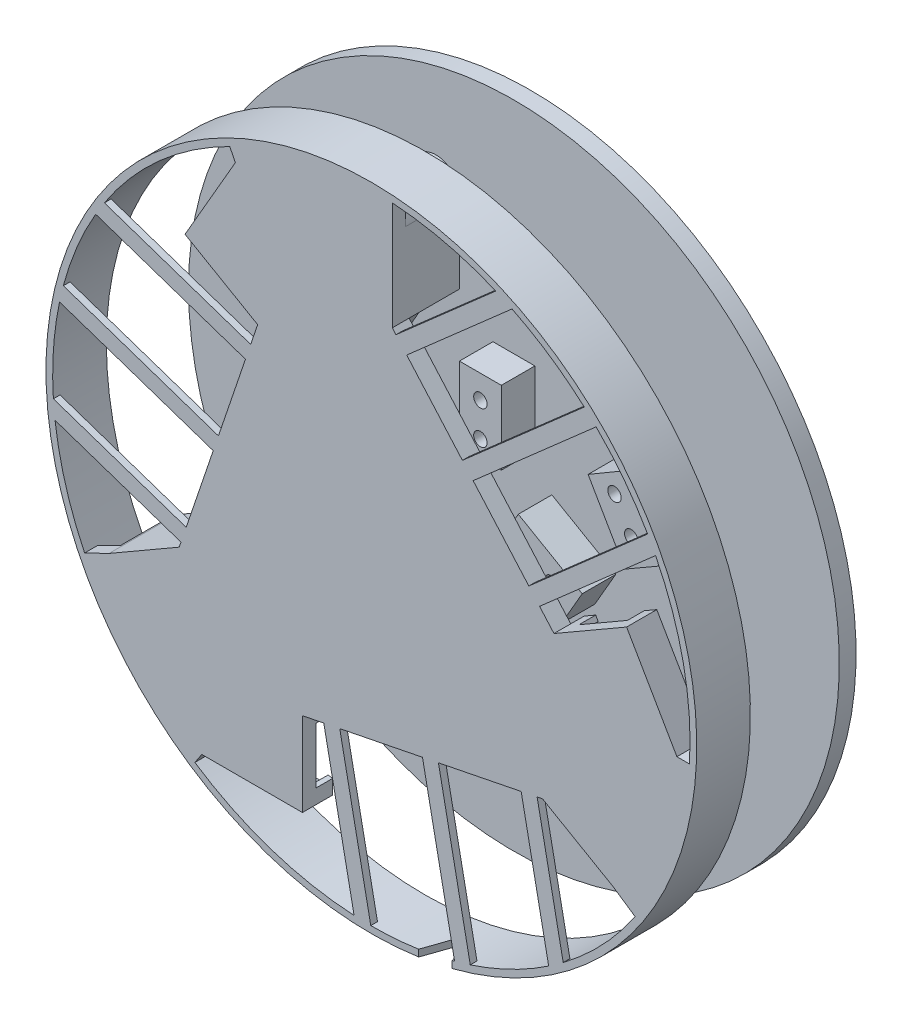
SolidWorks part; units mm, degrees
ref_plane "Alzado" through (0, 0, 0) normal (0, 0, 1) x (1, 0, 0)
ref_plane "Planta" through (0, 0, 0) normal (0, 1, 0) x (1, 0, 0)
ref_plane "Vista lateral" through (0, 0, 0) normal (1, 0, 0) x (0, 0, -1)
sketch "Croquis1" plane through (0, 0, 0) normal (0, 0, 1) x (1, 0, 0)
  line L4 (-284.6174, -30.3598) -> (-262.6174, -30.3598) construction
  line L13 (-262.6174, -17.8598) -> (-266.249, -17.8598) construction
  line L18 (-262.6174, -17.8598) -> (-262.6174, -30.3598) construction
  line L23 (-277.4005, -17.8598) -> (-284.5311, -17.8598) construction
  line L24 (-262.6174, -24.1098) -> (-284.5743, -24.1098) construction
  line L25 (-284.6174, -30.3598) -> (-284.5311, -17.8598) construction
  line L26 (-269.354, -5.2187) -> (-263.104, -16.044) construction
  line L27 (-284.6174, -30.3598) -> (-277.4005, -17.8598) construction
  line L35 (-252.0942, 76.5108) -> (-97.0942, 76.5108) construction
  line L36 (-97.0942, 76.5108) -> (-174.5942, 210.7447) construction
  line L37 (-174.5942, 210.7447) -> (-252.0942, 76.5108) construction
  line L38 (-282.1565, -12.6102) -> (-288.3318, -16.1755) construction
  line L39 (-282.1565, -27.044) -> (-288.3318, -16.1755) construction
  line L47 (-282.1565, -27.044) -> (-282.1565, -12.6102) construction
  line L48 (-282.1565, -12.6102) -> (-288.3318, -16.1755) construction
  line L49 (-266.229, -10.6313) -> (-285.2441, -21.6098) construction
  line L50 (-269.354, -5.2187) -> (-282.1565, -12.6102) construction
  line L51 (-266.229, -10.6313) -> (-285.2441, -21.6098) construction
  line L53 (-153.7083, -83.7331) -> (-164.7083, -64.6806) construction
  line L55 (-175.5336, -70.9306) -> (-173.7178, -74.0756) construction
  line L58 (-175.5336, -70.9306) -> (-164.7083, -64.6806) construction
  line L60 (-183.1128, -83.0851) -> (-176.8628, -72.2598) construction
  line L62 (-170.3103, -90.4767) -> (-164.135, -94.042) construction
  line L65 (-183.1128, -83.0851) -> (-170.3103, -90.4767) construction
  line L70 (-173.7178, -74.0756) -> (-176.8628, -72.2598) construction
  line L72 (-164.135, -94.042) -> (-162.1915, -95.164) construction
  line L73 (-152.6294, -85.6018) -> (-153.7083, -83.7331) construction
  line L75 (-168.142, -83.7331) -> (-164.5767, -89.9084) construction
  line L77 (-170.1209, -67.8056) -> (-159.1425, -86.8208) construction
  line L82 (-153.7083, -83.7331) -> (-164.5767, -89.9084) construction
  line L84 (-153.7083, -83.7331) -> (-168.142, -83.7331) construction
  line L85 (-170.3103, -90.4767) -> (-164.135, -94.042) construction
  line L87 (-157.8103, -83.2598) -> (-164.135, -94.042) construction
  line L88 (-285.2441, -21.6098) -> (-289.5743, -24.1098) construction
  line L89 (-284.5743, -24.1098) -> (-289.5743, -24.1098) construction
  line L90 (-266.249, -17.8598) -> (-263.104, -16.044) construction
  line L91 (-288.3318, -16.1755) -> (-290.2752, -17.2976) construction
  line L92 (-286.7752, -30.3598) -> (-284.6174, -30.3598) construction
  line L93 (-266.249, -17.8598) -> (-282.1565, -27.044) construction
  line L94 (-277.4005, -17.8598) -> (-266.249, -17.8598) construction
  line L95 (-157.8103, -83.2598) -> (-170.3103, -90.4767) construction
  line L96 (-179.9878, -77.6725) -> (-160.9726, -88.6509) construction
  line L97 (-179.9878, -77.6725) -> (-160.9726, -88.6509) construction
  line L98 (-160.9726, -88.6509) -> (-156.6425, -91.1509) construction
  line L99 (-159.1425, -86.8208) -> (-156.6425, -91.1509) construction
  line L100 (-173.7178, -74.0756) -> (-157.8103, -83.2598) construction
  line L101 (-168.142, -83.7331) -> (-173.7178, -74.0756) construction
  line L124 (-135.8442, 143.6277) -> (-252.0942, 76.5108) construction
  line L125 (-97.0942, 76.5108) -> (-213.3442, 143.6277) construction
  line L126 (-174.5942, 210.7447) -> (-174.5942, 76.5108) construction
  line L127 (-250.8517, 84.445) -> (-252.7951, 83.323)
  line L128 (-228.7489, 89.9892) -> (-247.7641, 79.0108) construction
  line L129 (-244.6764, 73.5765) -> (-250.8517, 84.445) construction
  line L130 (-228.7489, 89.9892) -> (-247.7641, 79.0108) construction
  line L137 (-231.8739, 95.4019) -> (-225.6239, 84.5765)
  line L138 (-231.8739, 95.4019) -> (-244.6764, 88.0103)
  line L139 (-225.1373, 76.5108) -> (-247.0942, 76.5108) construction
  line L140 (-247.7641, 79.0108) -> (-252.0942, 76.5108) construction
  line L142 (-247.0942, 76.5108) -> (-252.0942, 76.5108) construction
  line L143 (-244.6764, 73.5765) -> (-244.6764, 88.0103) construction
  line L144 (-247.1373, 70.2608) -> (-239.9205, 82.7608) construction
  line L146 (-225.1373, 82.7608) -> (-225.1373, 70.2608)
  line L148 (-247.1373, 70.2608) -> (-225.1373, 70.2608)
  line L149 (-228.7689, 82.7608) -> (-244.6764, 73.5765) construction
  line L150 (-225.1373, 82.7608) -> (-228.7689, 82.7608)
  line L151 (-228.7689, 82.7608) -> (-225.6239, 84.5765)
  line L152 (-244.6764, 88.0103) -> (-250.8517, 84.445)
  line L155 (-247.1373, 70.2608) -> (-247.051, 82.7608) construction
  line L156 (-244.6764, 88.0103) -> (-250.8517, 84.445) construction
  line L158 (-249.2951, 70.2608) -> (-247.1373, 70.2608)
  line L159 (-239.9205, 82.7608) -> (-247.051, 82.7608) construction
  line L161 (-239.9205, 82.7608) -> (-228.7689, 82.7608) construction
  line L162 (-180.8442, 187.4194) -> (-180.8442, 183.7879)
  line L165 (-168.3442, 183.7879) -> (-180.8442, 183.7879)
  line L167 (-168.3442, 198.571) -> (-168.3442, 205.7016) construction
  line L169 (-174.5942, 205.7447) -> (-174.5942, 210.7447) construction
  line L170 (-168.3442, 205.7016) -> (-168.3442, 207.9457)
  line L172 (-175.2684, 197.077) -> (-171.7031, 203.2522) construction
  line L173 (-188.0726, 187.3994) -> (-177.0942, 206.4146) construction
  line L175 (-174.5942, 183.7879) -> (-174.5942, 205.7447) construction
  line L176 (-168.3442, 198.571) -> (-168.3442, 205.7016)
  line L177 (-177.0942, 206.4146) -> (-174.5942, 210.7447) construction
  line L178 (-174.5942, 183.7879) -> (-174.5942, 205.7447) construction
  line L180 (-180.8442, 205.7879) -> (-168.3442, 205.7016) construction
  line L182 (-182.4853, 209.577) -> (-171.7031, 203.2522) construction
  line L183 (-180.8442, 187.4194) -> (-180.8442, 205.7879) construction
  line L185 (-168.3442, 183.7879) -> (-168.3442, 198.571)
  line L186 (-182.4853, 209.577) -> (-193.4853, 190.5244)
  line L189 (-182.4853, 209.577) -> (-175.2684, 197.077) construction
  line L191 (-175.2684, 197.077) -> (-180.8442, 187.4194) construction
  line L194 (-182.6599, 184.2744) -> (-180.8442, 187.4194)
  line L195 (-182.6599, 184.2744) -> (-193.4853, 190.5244)
  line L196 (-180.8442, 205.7879) -> (-168.3442, 198.571) construction
  line L197 (-181.4064, 211.4457) -> (-182.4853, 209.577)
  line L198 (-94.1599, 83.9285) -> (-108.5937, 83.9285) construction
  line L199 (-123.5645, 84.5765) -> (-110.7619, 77.185)
  line L200 (-110.7619, 77.185) -> (-104.5867, 73.6197) construction
  line L205 (-98.2619, 84.4019) -> (-104.5867, 73.6197) construction
  line L206 (-101.4243, 79.0108) -> (-97.0942, 76.5108) construction
  line L207 (-104.5867, 73.6197) -> (-102.6432, 72.4976)
  line L208 (-99.5942, 80.8409) -> (-97.0942, 76.5108) construction
  line L209 (-94.1599, 83.9285) -> (-105.1599, 102.9811)
  line L210 (-120.4395, 89.9892) -> (-101.4243, 79.0108) construction
  line L211 (-115.9853, 96.7311) -> (-105.1599, 102.9811)
  line L212 (-114.1695, 93.5861) -> (-117.3145, 95.4019)
  line L213 (-98.2619, 84.4019) -> (-110.7619, 77.185) construction
  line L214 (-93.081, 82.0598) -> (-94.1599, 83.9285)
  line L215 (-108.5937, 83.9285) -> (-114.1695, 93.5861) construction
  line L216 (-108.5937, 83.9285) -> (-105.0284, 77.7533) construction
  line L217 (-110.5726, 99.8561) -> (-99.5942, 80.8409) construction
  line L218 (-114.1695, 93.5861) -> (-98.2619, 84.4019) construction
  line L219 (-120.4395, 89.9892) -> (-101.4243, 79.0108) construction
  line L220 (-110.7619, 77.185) -> (-104.5867, 73.6197)
  line L221 (-94.1599, 83.9285) -> (-105.0284, 77.7533) construction
  line L222 (-123.5645, 84.5765) -> (-117.3145, 95.4019)
  line L223 (-115.9853, 96.7311) -> (-114.1695, 93.5861)
  line L224 (-247.7641, 79.0108) -> (-174.5942, 121.2554) construction
  line L225 (-247.7641, 79.0108) -> (-182.6599, 116.5987) construction
  line L226 (-102.6432, -54.2286) -> (-102.6432, -47.098) construction
  line L227 (-111.3932, -46.385) -> (-108.8932, -42.0549) construction
  line L228 (-116.959, -68.5252) -> (-115.1432, -65.3802) construction
  line L229 (-115.7054, -41.3539) -> (-116.7843, -43.2226) construction
  line L230 (-116.7843, -43.2226) -> (-109.5674, -55.7226) construction
  line L231 (-115.1432, -47.0117) -> (-102.6432, -54.2286) construction
  line L232 (-109.5674, -55.7226) -> (-106.0021, -49.5474) construction
  line L233 (-115.1432, -65.3802) -> (-115.1432, -69.0117) construction
  line L234 (-115.1432, -65.3802) -> (-115.1432, -47.0117) construction
  line L235 (-102.6432, -54.2286) -> (-102.6432, -47.098) construction
  line L236 (-108.8932, -47.0549) -> (-108.8932, -42.0549) construction
  line L237 (-102.6432, -69.0117) -> (-115.1432, -69.0117) construction
  line L238 (-108.8932, -69.0117) -> (-108.8932, -47.0549) construction
  line L239 (-102.6432, -69.0117) -> (-102.6432, -54.2286) construction
  line L240 (-109.5674, -55.7226) -> (-115.1432, -65.3802) construction
  line L241 (-115.1432, -47.0117) -> (-102.6432, -47.098) construction
  line L242 (-108.8932, -69.0117) -> (-108.8932, -47.0549) construction
  line L243 (-116.959, -68.5252) -> (-127.7843, -62.2752) construction
  line L244 (-102.6432, -47.098) -> (-102.6432, -44.8539) construction
  line L245 (-116.7843, -43.2226) -> (-106.0021, -49.5474) construction
  line L246 (-116.7843, -43.2226) -> (-127.7843, -62.2752) construction
  line L247 (-122.3716, -65.4002) -> (-111.3932, -46.385) construction
  line L248 (-172.9402, 56.3242) -> (-183.9402, 37.2716) construction
  line L249 (-173.1149, 31.0216) -> (-171.2991, 34.1666) construction
  line L250 (-173.1149, 31.0216) -> (-183.9402, 37.2716) construction
  line L251 (-158.7991, 30.5351) -> (-171.2991, 30.5351) construction
  line L252 (-158.7991, 45.3182) -> (-158.7991, 52.4488) construction
  line L253 (-158.7991, 30.5351) -> (-158.7991, 45.3182) construction
  line L254 (-171.2991, 34.1666) -> (-171.2991, 30.5351) construction
  line L255 (-158.7991, 52.4488) -> (-158.7991, 54.6929) construction
  line L256 (-171.8613, 58.1929) -> (-172.9402, 56.3242) construction
  line L257 (-165.7233, 43.8242) -> (-162.158, 49.9995) construction
  line L258 (-178.5275, 34.1466) -> (-167.5491, 53.1618) construction
  line L259 (-172.9402, 56.3242) -> (-162.158, 49.9995) construction
  line L260 (-172.9402, 56.3242) -> (-165.7233, 43.8242) construction
  line L261 (-158.7991, 45.3182) -> (-158.7991, 52.4488) construction
  line L262 (-171.2991, 52.5351) -> (-158.7991, 52.4488) construction
  line L263 (-171.2991, 52.5351) -> (-158.7991, 45.3182) construction
  line L264 (-165.0491, 30.5351) -> (-165.0491, 52.492) construction
  line L265 (-165.0491, 30.5351) -> (-165.0491, 52.492) construction
  line L266 (-165.0491, 52.492) -> (-165.0491, 57.492) construction
  line L267 (-167.5491, 53.1618) -> (-165.0491, 57.492) construction
  line L268 (-171.2991, 34.1666) -> (-171.2991, 52.5351) construction
  line L269 (-165.7233, 43.8242) -> (-171.2991, 34.1666) construction
  circle A2 centre (-269.6174, -24.1098) radius 2 construction
  circle A3 centre (-279.6174, -24.1098) radius 2 construction
  circle A25 centre (-272.2911, -14.1313) radius 2 construction
  circle A26 centre (-280.9514, -19.1313) radius 2 construction
  arc A27 (-286.7752, -30.3598) -> (-290.2752, -17.2976) centre (-286.7752, -23.3598) cw construction
  circle A28 centre (-166.6209, -73.8677) radius 2 construction
  circle A29 centre (-161.6209, -82.528) radius 2 construction
  circle A30 centre (-173.9256, -81.1725) radius 2 construction
  circle A31 centre (-165.2654, -86.1725) radius 2 construction
  arc A32 (-152.6294, -85.6018) -> (-162.1915, -95.164) centre (-158.6915, -89.1018) cw construction
  circle A54 centre (-234.811, 86.4892) radius 2
  circle A55 centre (-243.4713, 81.4892) radius 2
  circle A56 centre (-232.1373, 76.5108) radius 2
  circle A57 centre (-242.1373, 76.5108) radius 2
  arc A58 (-249.2951, 70.2608) -> (-252.7951, 83.323) centre (-249.2951, 77.2608) cw
  circle A59 centre (-179.5726, 202.1218) radius 2
  circle A60 centre (-174.5942, 190.7879) radius 2
  circle A61 centre (-184.5726, 193.4616) radius 2
  arc A62 (-181.4064, 211.4457) -> (-168.3442, 207.9457) centre (-175.3442, 207.9457) cw
  circle A63 centre (-174.5942, 200.7879) radius 2
  circle A64 centre (-102.0726, 85.1337) radius 2
  circle A65 centre (-107.0726, 93.7939) radius 2
  circle A66 centre (-105.7171, 81.4892) radius 2
  circle A67 centre (-114.3773, 86.4892) radius 2
  arc A68 (-93.081, 82.0598) -> (-102.6432, 72.4976) centre (-99.1432, 78.5598) cw
  circle A69 centre (-174.5942, 121.2554) radius 9.3135
  circle A71 centre (-108.8932, -62.0117) radius 2 construction
  circle A72 centre (-118.8716, -59.338) radius 2 construction
  circle A73 centre (-113.8716, -50.6778) radius 2 construction
  circle A74 centre (-108.8932, -52.0117) radius 2 construction
  arc A75 (-115.7054, -41.3539) -> (-102.6432, -44.8539) centre (-109.6432, -44.8539) cw construction
  circle A76 centre (-175.0275, 40.2088) radius 2 construction
  circle A77 centre (-170.0275, 48.8691) radius 2 construction
  circle A78 centre (-165.0491, 37.5351) radius 2 construction
  circle A79 centre (-165.0491, 47.5351) radius 2 construction
  arc A80 (-171.8613, 58.1929) -> (-158.7991, 54.6929) centre (-165.7991, 54.6929) cw construction
  point P1 (-145.4363, 273.9919)
  point P88 (-203.7553, -19.2562)
  dimension "D10" = 30
  dimension "D12" = 4
  dimension "D13" = 5
  dimension "D9" = 7
  dimension "D14" = 5
  dimension "D16" = 7
  dimension "D2" = 5
  dimension "D3" = 60
  dimension "D4" = 5
  dimension "D5" = 30
  dimension "D6" = 22
  dimension "D7" = 60
  dimension "D8" = 155
  dimension "D11" = 10
  dimension "D15" = 30
  dimension "D17" = 30
extrude "Saliente-Extruir2" add sketch "Croquis1" along normal blind 20
sketch "Croquis2" plane through (0, 0, 20) normal (0, 0, 1) x (1, 0, 0)
  line L0 (-105.1599, 102.9811) -> (-120.1599, 128.9619)
  line L1 (-225.1373, 70.2608) -> (-195.1373, 70.2608)
  line L3 (-225.1373, 45.2608) -> (-195.1373, 45.2608)
  line L4 (-195.1373, 70.2608) -> (-195.1373, 45.2608)
  line L5 (-120.1599, 128.9619) -> (-98.5093, 141.4619)
  line L6 (-98.5093, 141.4619) -> (-83.5093, 115.4811)
  line L8 (-193.4853, 190.5244) -> (-208.4853, 164.5436)
  line L9 (-208.4853, 164.5436) -> (-230.1359, 177.0436)
  line L10 (-230.1359, 177.0436) -> (-217.349, 199.1913)
  line L11 (-217.349, 199.1913) -> (-215.1359, 203.0244)
  line L13 (-168.3442, 207.9457) -> (-168.3442, 216.0496)
  line L14 (-215.1359, 203.0244) -> (-216.7938, 206.3682)
  line L15 (-252.7951, 83.323) -> (-260.0693, 79.7945)
  line L16 (-225.1373, 45.2608) -> (-227.2042, 42.1531)
  line L17 (-83.5093, 115.4811) -> (-79.7698, 115.4811)
  line L18 (-102.6432, 72.4976) -> (-95.9504, 67.9623)
  line L19 (-102.6432, 72.4976) -> (-94.499, 84.5159)
  line L20 (-93.081, 82.0598) -> (-105.1599, 102.9811) construction
  line L21 (-94.499, 84.5159) -> (-105.1599, 102.9811)
  line L22 (-225.1373, 70.2608) -> (-249.2951, 70.2608)
  line L23 (-249.2951, 70.2608) -> (-252.7951, 83.323)
  line L24 (-193.4853, 190.5244) -> (-182.6599, 184.2744)
  line L25 (-182.6599, 184.2744) -> (-180.8442, 187.4194)
  line L26 (-180.8442, 187.4194) -> (-180.8442, 183.7879)
  line L27 (-180.8442, 183.7879) -> (-168.3442, 183.7879)
  line L28 (-168.3442, 183.7879) -> (-168.3442, 207.9457)
  arc A0 (-79.7698, 115.4811) -> (-168.3442, 216.0496) centre (-174.5942, 121.2554) ccw
  circle A1 centre (-174.5942, 121.2554) radius 97
  arc A2 (-216.7938, 206.3682) -> (-260.0693, 79.7945) centre (-174.5942, 121.2554) ccw
  arc A3 (-227.2042, 42.1531) -> (-95.9504, 67.9623) centre (-174.5942, 121.2554) ccw
  dimension "D1" = 190
  dimension "D2" = 2
  dimension "D3" = 30
  dimension "D4" = 25
  dimension "D5" = 30
  dimension "D6" = 25
  dimension "D7" = 30
  dimension "D8" = 25
  dimension "D9" = 30
extrude "Saliente-Extruir3" add sketch "Croquis2" against normal blind 4
sketch "Croquis3" plane through (0, 0, 0) normal (0, 0, -1) x (-1, 0, 0)
  circle A0 centre (174.5942, 200.7879) radius 2
  circle A3 centre (179.5726, 202.1218) radius 2
  circle A4 centre (184.5726, 193.4616) radius 2
  circle A5 centre (174.5942, 190.7879) radius 2
extrude "Cortar-Extruir2" cut sketch "Croquis3" against normal blind 36
sketch "Croquis4" plane through (0, 0, 20) normal (0, 0, 1) x (1, 0, 0)
  line L0 (-110.746, 83.0522) -> (-110.7165, 81.4124)
  line L1 (-173.4333, 195.6512) -> (-172.0279, 196.4967)
  line L2 (-107.0309, 88.7941) -> (-109.4032, 86.9969)
  line L3 (-180.2635, 195.9976) -> (-177.5209, 194.8418)
  line L4 (-183.5776, 199.1284) -> (-183.7476, 198.393)
  line L5 (-102.6625, 90.0987) -> (-103.2144, 90.6137)
  line L6 (-239.6033, 85.0629) -> (-241.0381, 85.8572)
  line L7 (-236.4882, 78.9745) -> (-236.8585, 81.9276)
  line L8 (-237.5425, 74.5391) -> (-236.8206, 74.7596)
  arc A0 (-183.7476, 198.393) -> (-180.2635, 195.9976) centre (-184.5726, 193.4616) ccw
  arc A1 (-177.5209, 194.8418) -> (-173.4333, 195.6512) centre (-174.5942, 190.7879) ccw
  arc A2 (-175.9744, 205.5936) -> (-183.5776, 199.1284) centre (-179.5726, 202.1218) ccw
  arc A4 (-103.2144, 90.6137) -> (-107.0309, 88.7941) centre (-107.0726, 93.7939) ccw
  arc A5 (-109.4032, 86.9969) -> (-110.746, 83.0522) centre (-114.3773, 86.4892) ccw
  arc A6 (-172.0279, 196.4967) -> (-175.9744, 205.5936) centre (-174.5942, 200.7879) ccw
  arc A7 (-100.8651, 80.2817) -> (-102.6625, 90.0987) centre (-102.0726, 85.1337) ccw
  arc A8 (-110.7165, 81.4124) -> (-100.8651, 80.2817) centre (-105.7171, 81.4892) ccw
  arc A9 (-236.8206, 74.7596) -> (-236.4882, 78.9745) centre (-232.1373, 76.5108) ccw
  arc A10 (-236.8585, 81.9276) -> (-239.6033, 85.0629) centre (-234.811, 86.4892) ccw
  arc A11 (-246.943, 77.891) -> (-237.5425, 74.5391) centre (-242.1373, 76.5108) ccw
  arc A12 (-241.0381, 85.8572) -> (-246.943, 77.891) centre (-243.4713, 81.4892) ccw
  point P40 (-174.5942, 121.2554)
  dimension "D1" = 10
  dimension "D2" = 10
  dimension "D3" = 3
sketch "Croquis5" plane through (0, 0, 16) normal (0, 0, -1) x (-1, 0, 0)
  line L1 (83.5093, 115.4811) -> (98.5093, 141.4619)
  line L2 (98.5093, 141.4619) -> (102.2503, 139.302)
  line L3 (120.1599, 128.9619) -> (98.5093, 141.4619) construction
  line L4 (116.7163, 130.95) -> (120.1599, 128.9619)
  line L5 (120.1599, 128.9619) -> (96.8471, 88.5828)
  line L6 (98.5093, 137.5214) -> (84.7655, 113.7667)
  line L7 (98.5093, 137.5214) -> (99.5395, 139.302)
  line L8 (99.5395, 139.302) -> (101.7362, 138.0311)
  line L9 (101.7362, 138.0311) -> (102.2503, 139.302)
  line L11 (116.7163, 130.95) -> (115.9702, 129.6577)
  line L12 (115.9702, 129.6577) -> (118.0912, 128.4331)
  line L13 (118.0912, 128.4331) -> (95.5245, 89.3464)
  line L14 (95.5245, 89.3464) -> (96.8471, 88.5828)
  line L16 (116.7163, 130.95) -> (120.1599, 128.9619)
  line L17 (215.1359, 203.0244) -> (230.1359, 177.0436)
  line L18 (230.1359, 177.0436) -> (226.3949, 174.8838)
  line L19 (211.9289, 166.5318) -> (208.4853, 164.5436)
  line L20 (208.4853, 164.5436) -> (185.1724, 204.9227)
  line L21 (226.7233, 179.0139) -> (213.0231, 202.7937)
  line L22 (226.7233, 179.0139) -> (227.7503, 177.2314)
  line L23 (227.7503, 177.2314) -> (225.5514, 175.9645)
  line L24 (225.5514, 175.9645) -> (226.3949, 174.8838)
  line L25 (211.9289, 166.5318) -> (211.1828, 167.8242)
  line L26 (211.1828, 167.8242) -> (209.0617, 166.5996)
  line L27 (209.0617, 166.5996) -> (186.495, 205.6863)
  line L28 (186.495, 205.6863) -> (185.1724, 204.9227)
  line L30 (211.9289, 166.5318) -> (208.4853, 164.5436)
  line L32 (225.1373, 45.2608) -> (195.1373, 45.2608)
  line L33 (195.1373, 45.2608) -> (195.1373, 49.5805)
  line L34 (195.1373, 66.2844) -> (195.1373, 70.2608)
  line L35 (195.1373, 70.2608) -> (241.763, 70.2608)
  line L36 (198.5499, 47.231) -> (225.994, 47.2058)
  line L37 (198.5499, 47.231) -> (196.4927, 47.2329)
  line L38 (196.4927, 47.2329) -> (196.495, 49.7707)
  line L39 (196.495, 49.7707) -> (195.1373, 49.5805)
  line L40 (195.1373, 66.2844) -> (196.6296, 66.2844)
  line L41 (196.6296, 66.2844) -> (196.6296, 68.7336)
  line L42 (196.6296, 68.7336) -> (241.763, 68.7336)
  line L43 (241.763, 68.7336) -> (241.763, 70.2608)
  line L45 (195.1373, 66.2844) -> (195.1373, 70.2608)
  line L48 (225.1373, 45.2608) -> (225.994, 47.2058)
  line L49 (83.5093, 115.4811) -> (84.7655, 113.7667)
  line L50 (215.1359, 203.0244) -> (213.0231, 202.7937)
  point P51 (174.5942, 121.2554)
  line M15 (93.081, 82.0598) -> (105.1599, 102.9811)
  line M16 (105.1599, 102.9811) -> (120.1599, 128.9619)
  line M17 (120.1599, 128.9619) -> (98.5093, 141.4619)
  line M23 (181.4064, 211.4457) -> (193.4853, 190.5244)
  line M24 (193.4853, 190.5244) -> (208.4853, 164.5436)
  line M25 (208.4853, 164.5436) -> (230.1359, 177.0436)
  line M26 (230.1359, 177.0436) -> (215.1359, 203.0244)
  line M31 (249.2951, 70.2608) -> (225.1373, 70.2608)
  line M32 (225.1373, 70.2608) -> (195.1373, 70.2608)
  line M33 (195.1373, 70.2608) -> (195.1373, 45.2608)
  dimension "D1" = 3
extrude "Saliente-Extruir6" add sketch "Croquis5" along normal blind 5 contours L42 L43 L40 L41 M31 M32 M33 | L13 L14 L11 L12 M15 M16 M17 | L27 L28 L25 L26 M23 M24 M25 | L50 L21 L22 L23 L24 M26 M25 | L36 L48 L32 L33 L39 L38 L37 | L1 L2 L9 L8 L7 L6 L49
sketch "Croquis6" plane through (0, 0, 16) normal (0, 0, -1) x (-1, 0, 0)
  circle A0 centre (174.5942, 121.2554) radius 97
  circle A1 centre (174.5942, 121.2554) radius 95
extrude "Saliente-Extruir7" add sketch "Croquis6" along normal blind 35
sketch "Croquis7" plane through (0, 0, 20) normal (0, 0, 1) x (1, 0, 0)
  line L1 (-191.2527, 143.6517) -> (-154.7152, 143.6517)
  line L2 (-191.2527, 143.6517) -> (-191.2527, 92.2383)
  line L3 (-191.2527, 92.2383) -> (-154.7152, 92.2383)
  line L4 (-154.7152, 143.6517) -> (-154.7152, 92.2383)
extrude "Cortar-Extruir6" cut sketch "Croquis7" against normal through all
sketch "Croquis9" plane through (0, 0, 20) normal (0, 0, 1) x (1, 0, 0)
  line L1 (-195.1373, 70.2608) -> (-123.5645, 84.5765)
  line L2 (-231.8739, 95.4019) -> (-208.4853, 164.5436)
  line L3 (-208.4853, 164.5436) -> (-193.4853, 190.5244)
  line L4 (-231.8739, 95.4019) -> (-225.6239, 84.5765)
  line L5 (-225.6239, 84.5765) -> (-228.7689, 82.7608)
  line L6 (-228.7689, 82.7608) -> (-225.1373, 82.7608)
  line L7 (-225.1373, 70.2608) -> (-195.1373, 70.2608)
  line L8 (-123.5645, 84.5765) -> (-117.3145, 95.4019)
  line L9 (-117.3145, 95.4019) -> (-114.1695, 93.5861)
  line L10 (-114.1695, 93.5861) -> (-115.9853, 96.7311)
  line L11 (-115.9853, 96.7311) -> (-105.1599, 102.9811)
  line L12 (-105.1599, 102.9811) -> (-120.1599, 128.9619)
  line L13 (-193.4853, 190.5244) -> (-182.6599, 184.2744)
  line L14 (-182.6599, 184.2744) -> (-180.8442, 187.4194)
  line L15 (-180.8442, 187.4194) -> (-180.8442, 183.7879)
  line L16 (-180.8442, 183.7879) -> (-168.3442, 183.7879)
  line L17 (-168.3442, 183.7879) -> (-120.1599, 128.9619)
  line L46 (-102.6432, 72.4976) -> (-123.5645, 84.5765)
  line L47 (-95.9504, 67.9623) -> (-102.6432, 72.4976)
  line L48 (-225.1373, 45.2608) -> (-227.2042, 42.1531)
  line L49 (-195.1373, 45.2608) -> (-225.1373, 45.2608)
  line L50 (-195.1373, 70.2608) -> (-195.1373, 45.2608)
  line L51 (-225.1373, 70.2608) -> (-195.1373, 70.2608)
  line L52 (-225.1373, 82.7608) -> (-225.1373, 70.2608)
  line L53 (-228.7689, 82.7608) -> (-225.1373, 82.7608)
  line L54 (-225.6239, 84.5765) -> (-228.7689, 82.7608)
  line L55 (-231.8739, 95.4019) -> (-225.6239, 84.5765)
  line L56 (-252.7951, 83.323) -> (-231.8739, 95.4019)
  line L57 (-260.0693, 79.7945) -> (-252.7951, 83.323)
  line L58 (-215.1359, 203.0244) -> (-216.7938, 206.3682)
  line L59 (-230.1359, 177.0436) -> (-215.1359, 203.0244)
  line L60 (-208.4853, 164.5436) -> (-230.1359, 177.0436)
  line L61 (-193.4853, 190.5244) -> (-208.4853, 164.5436)
  line L62 (-182.6599, 184.2744) -> (-193.4853, 190.5244)
  line L63 (-180.8442, 187.4194) -> (-182.6599, 184.2744)
  line L64 (-180.8442, 183.7879) -> (-180.8442, 187.4194)
  line L65 (-168.3442, 183.7879) -> (-180.8442, 183.7879)
  line L66 (-168.3442, 216.0496) -> (-168.3442, 183.7879)
  line L67 (-83.5093, 115.4811) -> (-79.7698, 115.4811)
  line L68 (-98.5093, 141.4619) -> (-83.5093, 115.4811)
  line L69 (-120.1599, 128.9619) -> (-98.5093, 141.4619)
  line L70 (-105.1599, 102.9811) -> (-120.1599, 128.9619)
  line L71 (-115.9853, 96.7311) -> (-105.1599, 102.9811)
  line L72 (-114.1695, 93.5861) -> (-115.9853, 96.7311)
  line L73 (-117.3145, 95.4019) -> (-114.1695, 93.5861)
  line L74 (-123.5645, 84.5765) -> (-117.3145, 95.4019)
  line L81 (-225.1373, 82.7608) -> (-225.1373, 70.2608)
  arc A3 (-227.2042, 42.1531) -> (-95.9504, 67.9623) centre (-174.5942, 121.2554) ccw
  arc A4 (-216.7938, 206.3682) -> (-260.0693, 79.7945) centre (-174.5942, 121.2554) ccw
  arc A5 (-79.7698, 115.4811) -> (-168.3442, 216.0496) centre (-174.5942, 121.2554) ccw
  dimension "D1" = 0
extrude "Saliente-Extruir13" add sketch "Croquis9" against normal blind 3
sketch "Croquis12" plane through (0, 0, 20) normal (0, 0, 1) x (1, 0, 0)
  line L1 (-160.4827, 17.7717) -> (-150.4827, 17.7717)
  line L2 (-160.4827, 17.7717) -> (-160.4827, 34.5418)
  line L3 (-160.4827, 34.5418) -> (-150.4827, 34.5418)
  line L4 (-150.4827, 17.7717) -> (-150.4827, 34.5418)
  line L5 (-160.4827, 17.7717) -> (-150.4827, 34.5418) construction
  line L6 (-160.4827, 34.5418) -> (-150.4827, 17.7717) construction
  circle A0 centre (-174.5942, 121.2554) radius 97 construction
  point P0 (-155.4827, 26.1568)
  point P7 (-158.3956, 17.7717)
  dimension "D1" = 10
extrude "Cortar-Extruir7" cut sketch "Croquis12" against normal blind 10 draft 24
sketch "Croquis13" plane through (0, 0, 20) normal (0, 0, 1) x (1, 0, 0)
  line L0 (-147.4538, 160.0179) -> (-111.1268, 191.9441)
  line L1 (-120.1599, 128.9619) -> (-168.3442, 183.7879) construction
  line L2 (-144.2521, 156.3749) -> (-107.5871, 188.5982)
  line L3 (-147.4538, 160.0179) -> (-159.7883, 147.6835)
  line L4 (-159.7883, 147.6835) -> (-154.9344, 142.8297)
  line L5 (-154.9344, 142.8297) -> (-144.2521, 156.3749)
  line L6 (-111.1268, 191.9441) -> (-105.0801, 197.9909)
  line L7 (-105.0801, 197.9909) -> (-102.0567, 194.9675)
  line L8 (-107.5871, 188.5982) -> (-102.0567, 194.9675)
  line L9 (-221.7337, 125.3784) -> (-267.5461, 140.8754)
  line L10 (-220.1796, 129.9728) -> (-266.4183, 145.6139)
  line L11 (-221.7337, 125.3784) -> (-204.8845, 120.8637)
  line L12 (-204.8845, 120.8637) -> (-203.1079, 127.4941)
  line L13 (-203.1079, 127.4941) -> (-220.1796, 129.9728)
  line L14 (-267.5461, 140.8754) -> (-275.8061, 143.0887)
  line L15 (-275.8061, 143.0887) -> (-274.6995, 147.2187)
  line L16 (-266.4183, 145.6139) -> (-274.6995, 147.2187)
  line L17 (-154.5951, 78.3699) -> (-145.1096, 30.9467)
  line L18 (-159.3509, 77.4187) -> (-149.7772, 29.5542)
  line L19 (-154.5951, 78.3699) -> (-159.1098, 95.2191)
  line L20 (-159.1098, 95.2191) -> (-165.7402, 93.4425)
  line L21 (-165.7402, 93.4425) -> (-159.3509, 77.4187)
  line L22 (-145.1096, 30.9467) -> (-142.8964, 22.6867)
  line L23 (-142.8964, 22.6867) -> (-147.0264, 21.58)
  line L24 (-149.7772, 29.5542) -> (-147.0264, 21.58)
  line L25 (-167.2581, 182.5521) -> (-130.9312, 214.4783)
  line L26 (-164.0564, 178.909) -> (-127.3914, 211.1323)
  line L27 (-167.2581, 182.5521) -> (-179.5926, 170.2176)
  line L28 (-179.5926, 170.2176) -> (-174.7388, 165.3638)
  line L29 (-174.7388, 165.3638) -> (-164.0564, 178.909)
  line L30 (-130.9312, 214.4783) -> (-124.8844, 220.5251)
  line L31 (-124.8844, 220.5251) -> (-121.861, 217.5017)
  line L32 (-127.3914, 211.1323) -> (-121.861, 217.5017)
  line L33 (-147.4538, 160.0179) -> (-111.1268, 191.9441)
  line L34 (-144.2521, 156.3749) -> (-107.5871, 188.5982)
  line L35 (-147.4538, 160.0179) -> (-159.7883, 147.6835)
  line L36 (-159.7883, 147.6835) -> (-154.9344, 142.8297)
  line L37 (-154.9344, 142.8297) -> (-144.2521, 156.3749)
  line L38 (-111.1268, 191.9441) -> (-105.0801, 197.9909)
  line L39 (-105.0801, 197.9909) -> (-102.0567, 194.9675)
  line L40 (-107.5871, 188.5982) -> (-102.0567, 194.9675)
  line L41 (-127.6495, 137.4838) -> (-91.3225, 169.41)
  line L42 (-124.4477, 133.8407) -> (-87.7827, 166.064)
  line L43 (-127.6495, 137.4838) -> (-139.9839, 125.1493)
  line L44 (-139.9839, 125.1493) -> (-135.1301, 120.2955)
  line L45 (-135.1301, 120.2955) -> (-124.4477, 133.8407)
  line L46 (-91.3225, 169.41) -> (-85.2757, 175.4568)
  line L47 (-85.2757, 175.4568) -> (-82.2523, 172.4334)
  line L48 (-87.7827, 166.064) -> (-82.2523, 172.4334)
  line L49 (-231.3467, 96.9603) -> (-277.1591, 112.4573)
  line L50 (-229.7926, 101.5546) -> (-276.0313, 117.1958)
  line L51 (-231.3467, 96.9603) -> (-214.4975, 92.4456)
  line L52 (-214.4975, 92.4456) -> (-212.7209, 99.076)
  line L53 (-212.7209, 99.076) -> (-229.7926, 101.5546)
  line L54 (-277.1591, 112.4573) -> (-285.4191, 114.6705)
  line L55 (-285.4191, 114.6705) -> (-284.3125, 118.8006)
  line L56 (-276.0313, 117.1958) -> (-284.3125, 118.8006)
  line L57 (-221.7337, 125.3784) -> (-267.5461, 140.8754)
  line L58 (-220.1796, 129.9728) -> (-266.4183, 145.6139)
  line L59 (-221.7337, 125.3784) -> (-204.8845, 120.8637)
  line L60 (-204.8845, 120.8637) -> (-203.1079, 127.4941)
  line L61 (-203.1079, 127.4941) -> (-220.1796, 129.9728)
  line L62 (-267.5461, 140.8754) -> (-275.8061, 143.0887)
  line L63 (-275.8061, 143.0887) -> (-274.6995, 147.2187)
  line L64 (-266.4183, 145.6139) -> (-274.6995, 147.2187)
  line L65 (-212.1207, 153.7966) -> (-257.9331, 169.2935)
  line L66 (-210.5666, 158.3909) -> (-256.8053, 174.0321)
  line L67 (-212.1207, 153.7966) -> (-195.2715, 149.2818)
  line L68 (-195.2715, 149.2818) -> (-193.4949, 155.9123)
  line L69 (-193.4949, 155.9123) -> (-210.5666, 158.3909)
  line L70 (-257.9331, 169.2935) -> (-266.1931, 171.5068)
  line L71 (-266.1931, 171.5068) -> (-265.0865, 175.6368)
  line L72 (-256.8053, 174.0321) -> (-265.0865, 175.6368)
  line L73 (-125.1777, 84.2539) -> (-115.6923, 36.8307)
  line L74 (-129.9336, 83.3026) -> (-120.3599, 35.4381)
  line L75 (-125.1777, 84.2539) -> (-129.6925, 101.1031)
  line L76 (-129.6925, 101.1031) -> (-136.3229, 99.3264)
  line L77 (-136.3229, 99.3264) -> (-129.9336, 83.3026)
  line L78 (-115.6923, 36.8307) -> (-113.479, 28.5706)
  line L79 (-113.479, 28.5706) -> (-117.6091, 27.464)
  line L80 (-120.3599, 35.4381) -> (-117.6091, 27.464)
  line L81 (-154.5951, 78.3699) -> (-145.1096, 30.9467)
  line L82 (-159.3509, 77.4187) -> (-149.7772, 29.5542)
  line L83 (-154.5951, 78.3699) -> (-159.1098, 95.2191)
  line L84 (-159.1098, 95.2191) -> (-165.7402, 93.4425)
  line L85 (-165.7402, 93.4425) -> (-159.3509, 77.4187)
  line L86 (-145.1096, 30.9467) -> (-142.8964, 22.6867)
  line L87 (-142.8964, 22.6867) -> (-147.0264, 21.58)
  line L88 (-149.7772, 29.5542) -> (-147.0264, 21.58)
  line L89 (-184.0124, 72.486) -> (-174.527, 25.0628)
  line L90 (-188.7682, 71.5347) -> (-179.1945, 23.6702)
  line L91 (-184.0124, 72.486) -> (-188.5271, 89.3351)
  line L92 (-188.5271, 89.3351) -> (-195.1575, 87.5585)
  line L93 (-195.1575, 87.5585) -> (-188.7682, 71.5347)
  line L94 (-174.527, 25.0628) -> (-172.3137, 16.8027)
  line L95 (-172.3137, 16.8027) -> (-176.4437, 15.6961)
  line L96 (-179.1945, 23.6702) -> (-176.4437, 15.6961)
  line L97 (-154.5951, 78.3699) -> (-184.0124, 72.486) construction
  arc A0 (-79.7698, 115.4811) -> (-168.3442, 216.0496) centre (-174.5942, 121.2554) ccw construction
  point P32 (-174.5942, 121.2554)
  line M10 (-120.1599, 128.9619) -> (-168.3442, 183.7879)
  arc M12 (-168.3442, 216.0496) -> (-79.7698, 115.4811) centre (-174.5942, 121.2554) cw
  line M15 (-208.4853, 164.5436) -> (-231.8739, 95.4019)
  arc M18 (-260.0693, 79.7945) -> (-216.7938, 206.3682) centre (-174.5942, 121.2554) cw
  arc M43 (-95.9504, 67.9623) -> (-150.4827, 29.3662) centre (-174.5942, 121.2554) cw
  arc M47 (-160.4827, 27.3093) -> (-227.2042, 42.1531) centre (-174.5942, 121.2554) cw
  line M51 (-195.1373, 70.2608) -> (-123.5645, 84.5765)
  dimension "D7" = 30
  dimension "D1" = 2
  dimension "D2" = 2
  dimension "D3" = 2
  dimension "D4" = 2
  dimension "D5" = 2
  dimension "D6" = 2
extrude "Saliente-Extruir20" add sketch "Croquis13" against normal blind 2 contours L66 L65 M15 M18 | L10 L9 M15 M18 | L50 L49 M15 M18 | L2 L0 M10 M12 | L26 L25 M10 M12 | L42 L41 M10 M12 | L18 L17 M51 M43 | L90 L89 M51 M47 | L74 L73 M51 M43
sketch "Croquis14" plane through (0, 0, 17) normal (0, 0, -1) x (-1, 0, 0)
  line L0 (192.5407, 187.061) -> (182.2567, 181.1235)
  line L1 (229.0099, 96.6945) -> (206.7907, 162.3792)
  line L5 (168.6567, 180.6612) -> (122.8817, 128.5765)
  line L6 (122.8817, 128.5765) -> (108.6317, 103.8948)
  line L8 (206.7907, 162.3792) -> (192.5407, 187.061)
  line L9 (180.5317, 180.6612) -> (168.6567, 180.6612)
  line L10 (108.6317, 103.8948) -> (118.9157, 97.9573)
  line L12 (222.6102, 72.8105) -> (222.6102, 84.6855)
  line L13 (120.1785, 96.6945) -> (126.116, 86.4105)
  line L15 (126.116, 86.4105) -> (194.1102, 72.8105)
  line L16 (194.1102, 72.8105) -> (222.6102, 72.8105)
  line L17 (223.0724, 86.4105) -> (229.0099, 96.6945)
  line L18 (193.4853, 190.5244) -> (182.6599, 184.2744)
  line L19 (182.6599, 184.2744) -> (180.8442, 187.4194)
  line L20 (180.8442, 187.4194) -> (180.8442, 183.7879)
  line L21 (180.8442, 183.7879) -> (168.3442, 183.7879)
  line L22 (168.3442, 183.7879) -> (120.1599, 128.9619)
  line L23 (120.1599, 128.9619) -> (105.1599, 102.9811)
  line L24 (105.1599, 102.9811) -> (115.9853, 96.7311)
  line L25 (115.9853, 96.7311) -> (114.1695, 93.5861)
  line L26 (114.1695, 93.5861) -> (117.3145, 95.4019)
  line L27 (117.3145, 95.4019) -> (123.5645, 84.5765)
  line L28 (123.5645, 84.5765) -> (195.1373, 70.2608)
  line L29 (195.1373, 70.2608) -> (225.1373, 70.2608)
  line L30 (225.1373, 70.2608) -> (225.1373, 82.7608)
  line L31 (225.1373, 82.7608) -> (228.7689, 82.7608)
  line L32 (228.7689, 82.7608) -> (225.6239, 84.5765)
  line L33 (225.6239, 84.5765) -> (231.8739, 95.4019)
  line L34 (231.8739, 95.4019) -> (208.4853, 164.5436)
  line L35 (208.4853, 164.5436) -> (193.4853, 190.5244)
  line L36 (193.4853, 190.5244) -> (182.6599, 184.2744)
  line L37 (182.6599, 184.2744) -> (180.8442, 187.4194)
  line L38 (180.8442, 187.4194) -> (180.8442, 183.7879)
  line L39 (180.8442, 183.7879) -> (168.3442, 183.7879)
  line L40 (168.3442, 183.7879) -> (120.1599, 128.9619)
  line L41 (120.1599, 128.9619) -> (105.1599, 102.9811)
  line L42 (105.1599, 102.9811) -> (115.9853, 96.7311)
  line L43 (115.9853, 96.7311) -> (114.1695, 93.5861)
  line L44 (114.1695, 93.5861) -> (117.3145, 95.4019)
  line L45 (117.3145, 95.4019) -> (123.5645, 84.5765)
  line L46 (123.5645, 84.5765) -> (195.1373, 70.2608)
  line L47 (195.1373, 70.2608) -> (225.1373, 70.2608)
  line L48 (225.1373, 70.2608) -> (225.1373, 82.7608)
  line L49 (225.1373, 82.7608) -> (228.7689, 82.7608)
  line L50 (228.7689, 82.7608) -> (225.6239, 84.5765)
  line L51 (225.6239, 84.5765) -> (231.8739, 95.4019)
  line L52 (231.8739, 95.4019) -> (208.4853, 164.5436)
  line L53 (208.4853, 164.5436) -> (193.4853, 190.5244)
  line L54 (223.0724, 86.4105) -> (222.6102, 84.6855)
  line L55 (182.2567, 181.1235) -> (180.5317, 180.6612)
  line L56 (120.1785, 96.6945) -> (118.9157, 97.9573)
  dimension "D1" = 0
extrude "Saliente-Extruir22" add sketch "Croquis14" along normal blind 2
sketch "Croquis21" plane through (0, 0, 0) normal (0, 0, -1) x (-1, 0, 0)
  line L0 (40.9376, 91.3487) -> (26.5039, 91.3487) construction
  line L1 (11.5331, 91.9967) -> (24.3356, 84.6051)
  line L2 (24.3356, 84.6051) -> (30.5109, 81.0398) construction
  line L3 (36.8356, 91.822) -> (30.5109, 81.0398) construction
  line L4 (33.6733, 86.4309) -> (38.0034, 83.9309) construction
  line L5 (30.5109, 81.0398) -> (32.4543, 79.9178)
  line L6 (35.5034, 88.261) -> (38.0034, 83.9309) construction
  line L7 (40.9376, 91.3487) -> (29.9376, 110.4012)
  line L8 (14.6581, 97.4093) -> (33.6733, 86.4309) construction
  line L9 (19.1123, 104.1512) -> (29.9376, 110.4012)
  line L10 (20.9281, 101.0062) -> (17.7831, 102.822)
  line L11 (36.8356, 91.822) -> (24.3356, 84.6051) construction
  line L12 (42.0165, 89.48) -> (40.9376, 91.3487)
  line L13 (26.5039, 91.3487) -> (20.9281, 101.0062) construction
  line L14 (26.5039, 91.3487) -> (30.0691, 85.1734) construction
  line L15 (24.525, 107.2762) -> (35.5034, 88.261) construction
  line L16 (20.9281, 101.0062) -> (36.8356, 91.822) construction
  line L17 (14.6581, 97.4093) -> (33.6733, 86.4309) construction
  line L18 (24.3356, 84.6051) -> (30.5109, 81.0398)
  line L19 (40.9376, 91.3487) -> (30.0691, 85.1734) construction
  line L20 (11.5331, 91.9967) -> (17.7831, 102.822)
  line L21 (19.1123, 104.1512) -> (20.9281, 101.0062)
  line L22 (93.081, 82.0598) -> (105.1599, 102.9811)
  line L23 (105.1599, 102.9811) -> (131.6599, 148.8804)
  line L24 (131.6599, 148.8804) -> (140.975, 143.5024)
  line L25 (115.9853, 96.7311) -> (142.4853, 142.6304)
  line L26 (140.975, 143.5024) -> (142.4853, 142.6304)
  line L27 (102.6432, 72.4976) -> (123.5645, 84.5765)
  line L28 (105.1599, 102.9811) -> (93.081, 82.0598)
  line L29 (102.6432, 72.4976) -> (123.5645, 84.5765)
  line L30 (123.5645, 84.5765) -> (117.3145, 95.4019)
  line L31 (117.3145, 95.4019) -> (114.1695, 93.5861)
  line L32 (114.1695, 93.5861) -> (115.9853, 96.7311)
  line L33 (115.9853, 96.7311) -> (105.1599, 102.9811)
  line L34 (105.1599, 102.9811) -> (93.081, 82.0598)
  line L35 (102.6432, 72.4976) -> (123.5645, 84.5765)
  line L37 (117.3145, 95.4019) -> (114.1695, 93.5861)
  line L38 (114.1695, 93.5861) -> (115.9853, 96.7311)
  line L40 (163.2138, 121.9019) -> (169.4638, 111.0765)
  line L41 (131.6599, 148.8804) -> (105.1599, 102.9811)
  line L42 (181.4064, 211.4457) -> (193.4853, 190.5244)
  line L43 (193.4853, 190.5244) -> (219.9853, 144.6251)
  line L44 (219.9853, 144.6251) -> (210.6702, 139.247)
  line L45 (182.6599, 184.2744) -> (209.1599, 138.3751)
  line L52 (210.6702, 139.247) -> (209.1599, 138.3751)
  line L53 (168.3442, 207.9457) -> (168.3442, 183.7879)
  line L54 (193.4853, 190.5244) -> (181.4064, 211.4457)
  line L55 (168.3442, 207.9457) -> (168.3442, 183.7879)
  line L56 (180.8442, 183.7879) -> (180.8442, 187.4194)
  line L57 (180.8442, 187.4194) -> (182.6599, 184.2744)
  line L64 (123.5645, 84.5765) -> (169.4638, 111.0765)
  line L65 (180.8442, 130.7879) -> (168.3442, 130.7879)
  line L66 (117.3145, 95.4019) -> (163.2138, 121.9019)
  line L67 (219.9853, 144.6251) -> (193.4853, 190.5244)
  line L68 (168.3442, 183.7879) -> (168.3442, 130.7879)
  line L69 (180.8442, 183.7879) -> (180.8442, 130.7879)
  line L70 (249.2951, 70.2608) -> (225.1373, 70.2608)
  line L71 (225.1373, 70.2608) -> (172.1373, 70.2608)
  line L72 (172.1373, 70.2608) -> (172.1373, 81.0169)
  line L73 (225.1373, 82.7608) -> (172.1373, 82.7608)
  line L74 (172.1373, 81.0169) -> (172.1373, 82.7608)
  line L75 (252.7951, 83.323) -> (231.8739, 95.4019)
  line L76 (225.1373, 70.2608) -> (249.2951, 70.2608)
  line L77 (252.7951, 83.323) -> (231.8739, 95.4019)
  line L78 (225.6239, 84.5765) -> (228.7689, 82.7608)
  line L79 (228.7689, 82.7608) -> (225.1373, 82.7608)
  line L80 (179.7245, 111.0765) -> (185.9745, 121.9019)
  line L81 (172.1373, 70.2608) -> (225.1373, 70.2608)
  line L82 (231.8739, 95.4019) -> (185.9745, 121.9019)
  line L83 (225.6239, 84.5765) -> (179.7245, 111.0765)
  circle A0 centre (33.025, 92.5538) radius 2
  circle A1 centre (28.025, 101.2141) radius 2
  circle A2 centre (29.3805, 88.9093) radius 2
  circle A3 centre (20.7202, 93.9093) radius 2
  arc A4 (42.0165, 89.48) -> (32.4543, 79.9178) centre (35.9543, 85.98) cw
  arc A5 (181.4064, 211.4457) -> (168.3442, 207.9457) centre (175.3442, 207.9457) ccw
  arc A6 (93.081, 82.0598) -> (102.6432, 72.4976) centre (99.1432, 78.5598) ccw
  arc A7 (93.081, 82.0598) -> (102.6432, 72.4976) centre (99.1432, 78.5598) ccw
  arc A8 (249.2951, 70.2608) -> (252.7951, 83.323) centre (249.2951, 77.2608) ccw
  point P69 (174.5942, 121.2554)
  circle M34 centre (102.0726, 85.1337) radius 2
  circle M35 centre (114.3773, 86.4892) radius 2
  line M36 (105.1599, 102.9811) -> (93.081, 82.0598)
  arc M37 (93.081, 82.0598) -> (102.6432, 72.4976) centre (99.1432, 78.5598) ccw
  line M38 (102.6432, 72.4976) -> (123.5645, 84.5765)
  line M39 (123.5645, 84.5765) -> (117.3145, 95.4019)
  line M40 (117.3145, 95.4019) -> (114.1695, 93.5861)
  line M41 (114.1695, 93.5861) -> (115.9853, 96.7311)
  line M42 (115.9853, 96.7311) -> (105.1599, 102.9811)
  circle M43 centre (107.0726, 93.7939) radius 2
  circle M44 centre (105.7171, 81.4892) radius 2
  dimension "D4" = 53
  dimension "D5" = 53
  dimension "D1" = 0
extrude "Saliente-Extruir23" add sketch "Croquis21" along normal blind 12.5 contours L26 L24 L23 L25 M42 | L66 L64 L40 M39 | L70 A8 L75 L82 L80 L83 L78 L79 L73 L74 L72 L71 | L42 A5 L53 L68 L65 L69 L56 L57 L45 L52 L44 L43 | M42 M36 M37 M38 M39 M40 M41 M35 M43 M44 M34
sketch "Croquis26" plane through (0, 0, -12.5) normal (0, 0, -1) x (-1, 0, 0)
  line L0 (210.8442, 160.4579) -> (209.0284, 163.6029)
  line L1 (198.2031, 157.3529) -> (209.0284, 163.6029)
  line L2 (205.5947, 144.5503) -> (209.1599, 138.3751) construction
  line L3 (210.8442, 160.4579) -> (220.0284, 144.5503)
  line L5 (210.8442, 149.3063) -> (210.8442, 142.1757) construction
  line L6 (217.0942, 149.6326) -> (217.0942, 149.0894) construction
  line L7 (203.6158, 160.4779) -> (214.5942, 141.4627) construction
  line L8 (205.5947, 144.5503) -> (209.1599, 138.3751)
  line L9 (220.0284, 144.5503) -> (209.1599, 138.3751)
  line L10 (203.6158, 160.4779) -> (214.5942, 141.4627) construction
  line L11 (220.0284, 144.5503) -> (209.1599, 138.3751) construction
  line L12 (223.3442, 142.0894) -> (210.8442, 142.1757) construction
  line L13 (210.8442, 160.4579) -> (217.0942, 149.6326) construction
  line L14 (198.2031, 157.3529) -> (205.5947, 144.5503)
  line L16 (223.3442, 142.0894) -> (219.0818, 144.5503) construction
  line L17 (210.8442, 149.3063) -> (210.8442, 160.4579) construction
  line L20 (220.0284, 144.5503) -> (205.5947, 144.5503) construction
  line L22 (175.2684, 139.4125) -> (180.8442, 149.07) construction
  line L23 (217.0942, 145.6978) -> (217.0942, 145.0894) construction
  line L24 (168.3442, 137.9184) -> (168.3442, 130.7879)
  line L25 (217.0942, 144.5503) -> (217.0942, 142.1326) construction
  line L26 (182.4853, 126.9125) -> (171.7031, 133.2372) construction
  line L27 (180.8442, 130.7016) -> (168.3442, 130.7879)
  line L28 (180.8442, 149.07) -> (180.8442, 152.7016)
  line L29 (168.3442, 152.7016) -> (168.3442, 137.9184)
  line L30 (168.3442, 137.9184) -> (168.3442, 130.7879) construction
  line L31 (174.5942, 152.7016) -> (174.5942, 130.7447) construction
  line L32 (178.3031, 132.1687) -> (177.0942, 130.0748) construction
  line L33 (180.8442, 149.07) -> (180.8442, 136.57) construction
  line L34 (168.3442, 152.7016) -> (180.8442, 152.7016)
  line L35 (180.8442, 136.57) -> (180.5726, 136.0997) construction
  line L36 (175.2684, 139.4125) -> (171.7031, 133.2372) construction
  line L37 (182.4853, 126.9125) -> (180.0244, 131.1749) construction
  line L38 (180.8442, 149.07) -> (180.8442, 130.7016)
  line L39 (180.8442, 130.7016) -> (168.3442, 137.9184) construction
  line L40 (180.8442, 130.7016) -> (168.3442, 130.7879) construction
  line L41 (178.8768, 133.1625) -> (178.5726, 132.6356) construction
  line L42 (174.5942, 152.7016) -> (174.5942, 130.7447) construction
  line L43 (190.4195, 70.2608) -> (194.051, 70.2608)
  line L44 (194.051, 82.7608) -> (194.051, 70.2608)
  line L45 (190.4195, 70.2608) -> (172.051, 70.2608)
  line L46 (179.2679, 82.7608) -> (172.1373, 82.7608)
  line L47 (172.051, 70.2608) -> (172.1373, 82.7608)
  line L48 (194.051, 82.7608) -> (179.2679, 82.7608)
  line L49 (192.1498, 118.3366) -> (185.9745, 121.9019)
  line L50 (179.6498, 111.1197) -> (185.9745, 121.9019)
  line L51 (195.5573, 101.9355) -> (198.7023, 100.1197)
  line L52 (204.9523, 110.945) -> (192.1498, 118.3366)
  line L53 (204.9523, 110.945) -> (198.7023, 100.1197)
  line L54 (195.5573, 101.9355) -> (179.6498, 111.1197)
  line L55 (179.2679, 82.7608) -> (172.1373, 82.7608) construction
  line L56 (180.7619, 75.8366) -> (174.5867, 79.4019) construction
  line L57 (177.9195, 70.2608) -> (177.4491, 70.5324) construction
  line L58 (194.051, 76.5108) -> (172.0942, 76.5108) construction
  line L59 (194.051, 76.5108) -> (172.0942, 76.5108) construction
  line L60 (172.051, 70.2608) -> (172.1373, 82.7608) construction
  line L61 (168.2619, 68.6197) -> (174.5867, 79.4019) construction
  line L62 (190.4195, 70.2608) -> (177.9195, 70.2608) construction
  line L63 (168.2619, 68.6197) -> (172.5244, 71.0806) construction
  line L64 (180.7619, 75.8366) -> (190.4195, 70.2608) construction
  line L65 (172.051, 70.2608) -> (179.2679, 82.7608) construction
  line L66 (189.9815, 111.593) -> (195.5573, 101.9355) construction
  line L67 (174.5119, 72.2281) -> (173.985, 72.5324) construction
  line L68 (173.5182, 72.8019) -> (171.4243, 74.0108) construction
  line L69 (175.5478, 111.593) -> (186.4163, 117.7683) construction
  line L70 (192.1498, 118.3366) -> (185.9745, 121.9019) construction
  line L71 (201.8273, 105.5324) -> (182.8122, 116.5108) construction
  line L72 (182.1909, 112.5868) -> (180.982, 114.6807) construction
  line L73 (195.5573, 101.9355) -> (184.732, 108.1855) construction
  line L74 (184.732, 108.1855) -> (184.4604, 108.6558) construction
  line L75 (189.9815, 111.593) -> (186.4163, 117.7683) construction
  line L76 (175.5478, 111.593) -> (180.4696, 111.593) construction
  line L77 (179.6498, 111.1197) -> (192.1498, 118.3366) construction
  line L78 (179.6498, 111.1197) -> (185.9745, 121.9019) construction
  line L79 (182.7647, 111.593) -> (182.4604, 112.1199) construction
  line L80 (201.8273, 105.5324) -> (182.8122, 116.5108) construction
  line L81 (122.5189, 133.0476) -> (120.7031, 129.9026)
  line L82 (131.5284, 123.6526) -> (120.7031, 129.9026)
  line L83 (122.5189, 133.0476) -> (131.7031, 148.9552)
  line L84 (138.92, 136.4552) -> (142.4853, 142.6304)
  line L85 (131.7031, 148.9552) -> (142.4853, 142.6304)
  line L86 (131.5284, 123.6526) -> (138.92, 136.4552)
  line L87 (163.2886, 107.5113) -> (169.4638, 111.0765)
  line L88 (163.2886, 121.945) -> (169.4638, 111.0765)
  line L89 (147.381, 112.7608) -> (144.236, 110.945)
  line L90 (150.486, 100.1197) -> (163.2886, 107.5113)
  line L91 (150.486, 100.1197) -> (144.236, 110.945)
  line L92 (147.381, 112.7608) -> (163.2886, 121.945)
  line L93 (138.92, 136.4552) -> (142.4853, 142.6304) construction
  line L94 (132.1764, 138.6234) -> (138.3517, 142.1887) construction
  line L95 (128.7689, 143.8729) -> (129.2392, 144.1445) construction
  line L96 (126.1158, 126.7776) -> (137.0942, 145.7928) construction
  line L97 (126.1158, 126.7776) -> (137.0942, 145.7928) construction
  line L98 (131.7031, 148.9552) -> (142.4853, 142.6304) construction
  line L99 (132.1764, 153.0572) -> (138.3517, 142.1887) construction
  line L100 (122.5189, 133.0476) -> (128.7689, 143.8729) construction
  line L101 (132.1764, 153.0572) -> (132.1764, 148.1354) construction
  line L102 (132.1764, 138.6234) -> (122.5189, 133.0476) construction
  line L103 (131.7031, 148.9552) -> (138.92, 136.4552) construction
  line L104 (158.5326, 112.7608) -> (147.381, 112.7608) construction
  line L105 (132.1764, 145.8403) -> (132.7033, 146.1445) construction
  line L106 (133.1702, 146.4141) -> (135.2641, 147.6229) construction
  line L107 (165.7495, 125.2608) -> (165.6632, 112.7608) construction
  line L108 (163.2886, 107.5113) -> (169.4638, 111.0765) construction
  line L109 (147.361, 105.5324) -> (166.3762, 116.5108) construction
  line L110 (163.2886, 119.0108) -> (165.7063, 119.0108) construction
  line L111 (147.381, 112.7608) -> (158.2063, 119.0108) construction
  line L112 (158.2063, 119.0108) -> (158.7495, 119.0108) construction
  line L113 (158.5326, 112.7608) -> (165.6632, 112.7608) construction
  line L114 (165.7495, 125.2608) -> (163.2886, 120.9984) construction
  line L115 (163.2886, 121.945) -> (163.2886, 107.5113) construction
  line L116 (163.2886, 121.945) -> (169.4638, 111.0765) construction
  line L117 (162.1411, 119.0108) -> (162.7495, 119.0108) construction
  line L118 (147.361, 105.5324) -> (166.3762, 116.5108) construction
  circle A1 centre (207.1158, 154.4157) radius 2
  circle A4 centre (212.1158, 145.7554) radius 2
  circle A5 centre (174.5942, 135.7016) radius 2
  circle A6 centre (174.5942, 145.7016) radius 2
  circle A7 centre (187.051, 76.5108) radius 2
  circle A8 centre (177.051, 76.5108) radius 2
  circle A9 centre (187.1049, 114.0324) radius 2
  circle A10 centre (195.7652, 109.0324) radius 2
  circle A11 centre (129.6158, 132.8398) radius 2
  circle A12 centre (134.6158, 141.5001) radius 2
  circle A13 centre (162.0835, 114.0324) radius 2
  circle A14 centre (153.4232, 109.0324) radius 2
  point P135 (174.5942, 121.2554)
extrude "Saliente-Extruir25" add sketch "Croquis26" along normal blind 10
sketch "Croquis29" plane through (0, 0, -22.5) normal (0, 0, -1) x (-1, 0, 0)
  circle A0 centre (174.5942, 121.2554) radius 97
extrude "Saliente-Extruir26" add sketch "Croquis29" along normal blind 5
sketch "Croquis32" plane through (0, 0, -19) normal (0, 0, -1) x (-1, 0, 0)
  circle A0 centre (174.5942, 121.2554) radius 97
  circle A2 centre (174.5942, 121.2554) radius 95
extrude "Cortar-Extruir9" cut sketch "Croquis32" against normal blind 23
sketch "Croquis38" plane through (-168.3442, 0, 0) normal (1, 0, 0) x (0, 0, -1)
  line L1 (0, 183.7879) -> (12.5, 183.7879)
  line L2 (0, 183.7879) -> (0, 56.6139)
  line L3 (0, 56.6139) -> (12.5, 56.6139)
  line L4 (12.5, 183.7879) -> (12.5, 56.6139)
  line L5 (12.5, 183.7879) -> (0, 183.7879)
  line L6 (12.5, 183.7879) -> (12.5, 230.7715)
  line L7 (12.5, 230.7715) -> (0, 230.7715)
  line L8 (0, 183.7879) -> (0, 230.7715)
  line M5 (0, 183.7879) -> (0, 130.7879)
  line M6 (0, 130.7879) -> (12.5, 130.7879)
  line M10 (12.5, 152.7016) -> (12.5, 207.9457)
  line M11 (12.5, 207.9457) -> (-16, 207.9457)
extrude "Saliente-Extruir28" add sketch "Croquis4" against normal blind 1
extrude "Cortar-Extruir17" cut sketch "Croquis38" against normal blind 299 and the other way blind 202 contours L4 L1 M10 M5 M6 | L8 L1 M10 M11 | L8 L6 L7 M11 | L4 L2 L3 M6
